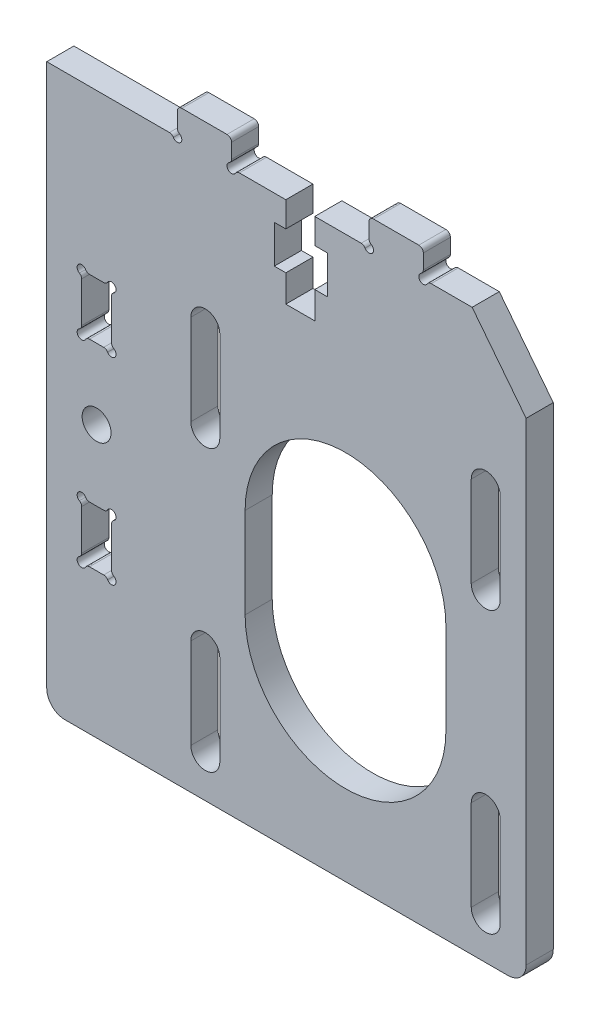
SolidWorks part; units mm, degrees
ref_plane "Front Plane" through (0, 0, 0) normal (0, 0, 1) x (1, 0, 0)
ref_plane "Top Plane" through (0, 0, 0) normal (0, 1, 0) x (1, 0, 0)
ref_plane "Right Plane" through (0, 0, 0) normal (1, 0, 0) x (0, 0, -1)
sketch "Model" plane through (0, 0, 0) normal (0, 0, 1) x (1, 0, 0)
  line L0 (295.0438, 218.1334) -> (281.4784, 218.1334)
  line L1 (295.9098, 220.6335) -> (295.9098, 218.9994)
  line L2 (301.4098, 221.1335) -> (296.4098, 221.1335)
  line L3 (301.9098, 218.9994) -> (301.9098, 220.6335)
  line L4 (307.9099, 218.1334) -> (302.7759, 218.1334)
  line L5 (307.9099, 215.3334) -> (307.9099, 218.1334)
  line L6 (306.6349, 215.3334) -> (307.9099, 215.3334)
  line L7 (306.6349, 211.1334) -> (306.6349, 215.3334)
  line L8 (307.9099, 211.1334) -> (306.6349, 211.1334)
  line L9 (307.9099, 208.1334) -> (307.9099, 211.1334)
  line L10 (311.1099, 208.1334) -> (307.9099, 208.1334)
  line L11 (311.1099, 211.1334) -> (311.1099, 208.1334)
  line L12 (312.5349, 211.1334) -> (311.1099, 211.1334)
  line L13 (312.5349, 215.3334) -> (312.5349, 211.1334)
  line L14 (311.1098, 215.3334) -> (312.5349, 215.3334)
  line L15 (311.1098, 218.1334) -> (311.1098, 215.3334)
  line L16 (316.2438, 218.1334) -> (311.1098, 218.1334)
  line L17 (317.1098, 220.6335) -> (317.1098, 218.9994)
  line L18 (322.6098, 221.1334) -> (317.6098, 221.1334)
  line L19 (323.1098, 218.9994) -> (323.1098, 220.6334)
  line L20 (328.5098, 218.1334) -> (323.9759, 218.1334)
  line L21 (334.4784, 210.489) -> (328.5098, 218.1334)
  line L22 (334.4784, 158.1334) -> (334.4784, 210.489)
  line L23 (283.4784, 156.1334) -> (332.4784, 156.1334)
  line L24 (281.4784, 218.1334) -> (281.4784, 158.1334)
  line L25 (325.6098, 176.1334) -> (325.6098, 186.1334)
  line L27 (303.4098, 176.1334) -> (303.4098, 186.1334)
  line L29 (331.6098, 160.6334) -> (331.6098, 170.6365)
  line L31 (328.4098, 160.6334) -> (328.4098, 170.6365)
  line L33 (331.6098, 201.6334) -> (331.6098, 191.6303)
  line L35 (328.4098, 201.6334) -> (328.4098, 191.6303)
  line L37 (297.4098, 160.6334) -> (297.4098, 170.6365)
  line L39 (300.6098, 160.6334) -> (300.6098, 170.6365)
  line L41 (297.4098, 201.6334) -> (297.4098, 191.6303)
  line L43 (300.6098, 201.6334) -> (300.6098, 191.6303)
  line L45 (288.6398, 173.0012) -> (288.6398, 177.4691)
  line L46 (286.2059, 172.1351) -> (287.7738, 172.1351)
  line L47 (285.3399, 199.2656) -> (285.3399, 194.7977)
  line L48 (287.7738, 200.1317) -> (286.2059, 200.1317)
  line L49 (288.6398, 194.7977) -> (288.6398, 199.2657)
  line L50 (286.2059, 193.9317) -> (287.7738, 193.9317)
  line L51 (287.7738, 178.3351) -> (286.2059, 178.3351)
  line L52 (285.3399, 177.4691) -> (285.3399, 173.0012)
  arc A0 (295.4768, 217.8834) -> (295.0438, 218.1334) centre (295.0438, 217.6334) ccw
  arc A1 (295.4768, 217.8834) -> (296.1598, 218.5664) centre (295.9098, 218.1334) ccw
  arc A2 (295.9098, 218.9994) -> (296.1598, 218.5664) centre (296.4098, 218.9994) ccw
  arc A3 (296.4098, 221.1335) -> (295.9098, 220.6335) centre (296.4098, 220.6335) ccw
  arc A4 (301.9098, 220.6335) -> (301.4098, 221.1335) centre (301.4098, 220.6335) ccw
  arc A5 (301.6598, 218.5664) -> (301.9098, 218.9994) centre (301.4098, 218.9994) ccw
  arc A6 (301.6598, 218.5664) -> (302.3429, 217.8834) centre (301.9098, 218.1334) ccw
  arc A7 (302.7759, 218.1334) -> (302.3429, 217.8834) centre (302.7759, 217.6334) ccw
  arc A8 (316.6768, 217.8834) -> (316.2438, 218.1334) centre (316.2438, 217.6334) ccw
  arc A9 (316.6768, 217.8834) -> (317.3598, 218.5664) centre (317.1098, 218.1334) ccw
  arc A10 (317.1098, 218.9994) -> (317.3598, 218.5664) centre (317.6098, 218.9994) ccw
  arc A11 (317.6098, 221.1334) -> (317.1098, 220.6335) centre (317.6098, 220.6334) ccw
  arc A12 (323.1098, 220.6334) -> (322.6098, 221.1334) centre (322.6098, 220.6334) ccw
  arc A13 (322.8598, 218.5664) -> (323.1098, 218.9994) centre (322.6098, 218.9994) ccw
  arc A14 (322.8598, 218.5664) -> (323.5429, 217.8834) centre (323.1098, 218.1334) ccw
  arc A15 (323.9759, 218.1334) -> (323.5429, 217.8834) centre (323.9759, 217.6334) ccw
  arc A16 (303.4098, 176.1334) -> (325.6098, 176.1334) centre (314.5098, 176.1334) ccw
  arc A18 (325.6098, 186.1334) -> (303.4098, 186.1334) centre (314.5098, 186.1334) ccw
  arc A20 (328.4098, 160.6334) -> (331.6098, 160.6334) centre (330.0098, 160.6334) ccw
  arc A22 (331.6098, 170.6365) -> (328.4098, 170.6365) centre (330.0098, 170.6365) ccw
  arc A24 (331.6098, 201.6334) -> (328.4098, 201.6334) centre (330.0098, 201.6334) ccw
  arc A26 (328.4098, 191.6303) -> (331.6098, 191.6303) centre (330.0098, 191.6303) ccw
  arc A28 (297.4098, 160.6334) -> (300.6098, 160.6334) centre (299.0098, 160.6334) ccw
  arc A30 (300.6098, 170.6365) -> (297.4098, 170.6365) centre (299.0098, 170.6365) ccw
  arc A32 (300.6098, 201.6334) -> (297.4098, 201.6334) centre (299.0098, 201.6334) ccw
  arc A34 (297.4098, 191.6303) -> (300.6098, 191.6303) centre (299.0098, 191.6303) ccw
  arc A36 (288.8898, 177.9021) -> (288.2068, 178.5851) centre (288.6398, 178.3351) ccw
  arc A37 (288.8898, 177.9021) -> (288.6398, 177.4691) centre (289.1398, 177.4691) ccw
  arc A38 (288.2068, 171.8851) -> (287.7738, 172.1351) centre (287.7738, 171.6351) ccw
  arc A39 (288.6398, 173.0012) -> (288.8898, 172.5682) centre (289.1398, 173.0012) ccw
  arc A40 (288.2068, 171.8851) -> (288.8898, 172.5682) centre (288.6398, 172.1351) ccw
  arc A41 (287.7738, 178.3351) -> (288.2068, 178.5851) centre (287.7738, 178.8351) ccw
  arc A42 (286.2059, 172.1351) -> (285.7729, 171.8851) centre (286.2059, 171.6351) ccw
  arc A43 (285.0899, 194.3647) -> (285.7729, 193.6817) centre (285.3399, 193.9317) ccw
  arc A44 (285.0899, 194.3647) -> (285.3399, 194.7977) centre (284.8399, 194.7977) ccw
  arc A45 (285.3399, 199.2656) -> (285.0899, 199.6987) centre (284.8399, 199.2656) ccw
  arc A46 (285.7729, 200.3817) -> (285.0899, 199.6987) centre (285.3399, 200.1317) ccw
  arc A47 (285.7729, 200.3817) -> (286.2059, 200.1317) centre (286.2059, 200.6317) ccw
  arc A48 (287.7738, 200.1317) -> (288.2068, 200.3817) centre (287.7738, 200.6317) ccw
  arc A49 (288.8898, 199.6987) -> (288.2068, 200.3817) centre (288.6398, 200.1317) ccw
  arc A50 (288.8898, 199.6987) -> (288.6398, 199.2657) centre (289.1398, 199.2656) ccw
  arc A51 (288.6398, 194.7977) -> (288.8898, 194.3647) centre (289.1398, 194.7977) ccw
  arc A52 (288.2068, 193.6817) -> (288.8898, 194.3647) centre (288.6398, 193.9317) ccw
  arc A53 (288.2068, 193.6817) -> (287.7738, 193.9317) centre (287.7738, 193.4317) ccw
  arc A54 (286.2059, 193.9317) -> (285.7729, 193.6817) centre (286.2059, 193.4317) ccw
  circle A55 centre (286.9898, 186.1334) radius 1.6
  arc A56 (285.0899, 172.5682) -> (285.7729, 171.8851) centre (285.3399, 172.1351) ccw
  arc A57 (285.3399, 177.4691) -> (285.0899, 177.9021) centre (284.8399, 177.4691) ccw
  arc A58 (285.0899, 172.5682) -> (285.3399, 173.0012) centre (284.8399, 173.0012) ccw
  arc A59 (285.7729, 178.5851) -> (285.0899, 177.9021) centre (285.3399, 178.3351) ccw
  arc A60 (285.7729, 178.5851) -> (286.2059, 178.3351) centre (286.2059, 178.8351) ccw
  arc A61 (281.4784, 158.1334) -> (283.4784, 156.1334) centre (283.4784, 158.1334) ccw
  arc A62 (332.4784, 156.1334) -> (334.4784, 158.1334) centre (332.4784, 158.1334) ccw
  point P150 (323.1098, 219.8164)
extrude "Boss-Extrude1" add sketch "Model" along normal blind 3
